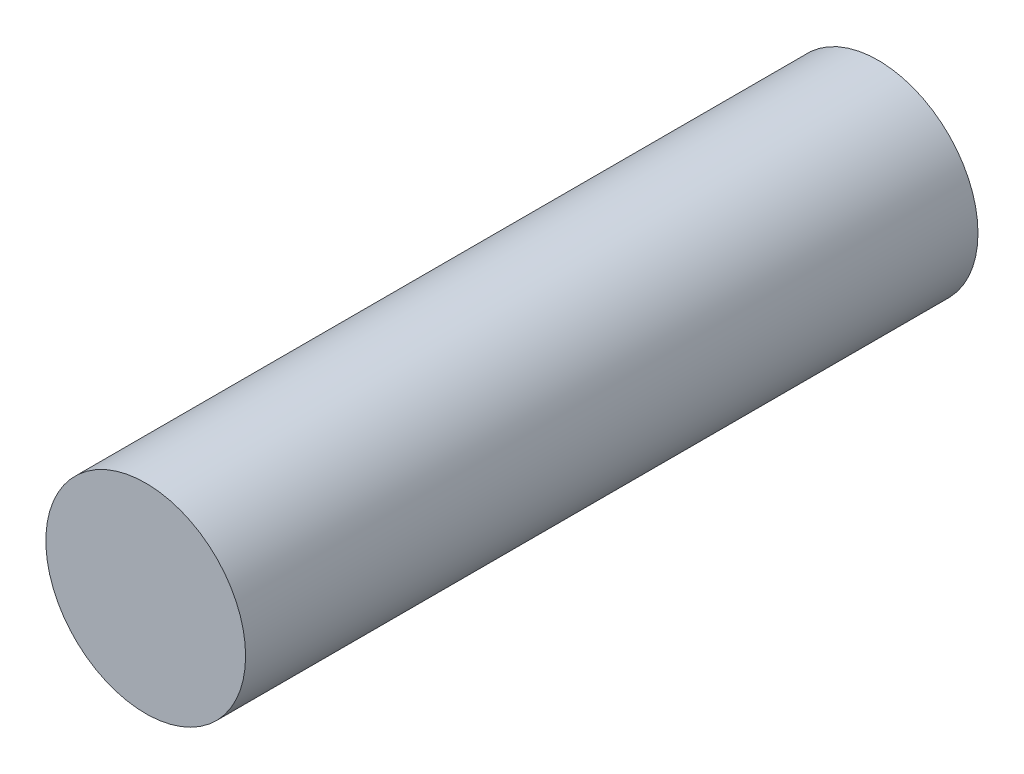
SolidWorks part; units mm, degrees
ref_plane "Front Plane" through (0, 0, 0) normal (0, 0, 1) x (1, 0, 0)
ref_plane "Top Plane" through (0, 0, 0) normal (0, 1, 0) x (1, 0, 0)
ref_plane "Right Plane" through (0, 0, 0) normal (1, 0, 0) x (0, 0, -1)
sketch "Sketch1" plane through (0, 0, 0) normal (0, 0, 1) x (1, 0, 0)
  circle A0 centre (0, 0) radius 15
  dimension "D1" = 30
extrude "Boss-Extrude1" add sketch "Sketch1" along normal blind 110
